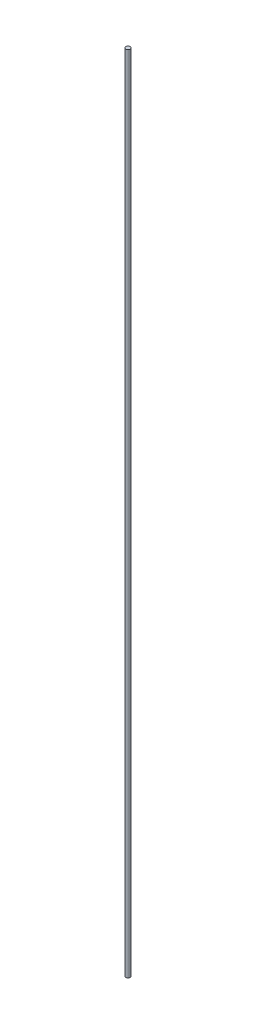
SolidWorks part; units mm, degrees
ref_plane "Ön Düzlem" through (0, 0, 0) normal (0, 0, 1) x (1, 0, 0)
ref_plane "Üst Düzlem" through (0, 0, 0) normal (0, 1, 0) x (1, 0, 0)
ref_plane "Sağ Düzlem" through (0, 0, 0) normal (1, 0, 0) x (0, 0, -1)
sketch "Çizim1" plane through (0, 0, 0) normal (0, 1, 0) x (1, 0, 0)
  circle A0 centre (0, 0) radius 4
  dimension "D1" = 8
extrude "Yükseklik-Ekstrüzyon1" add sketch "Çizim1" along normal blind 1400
